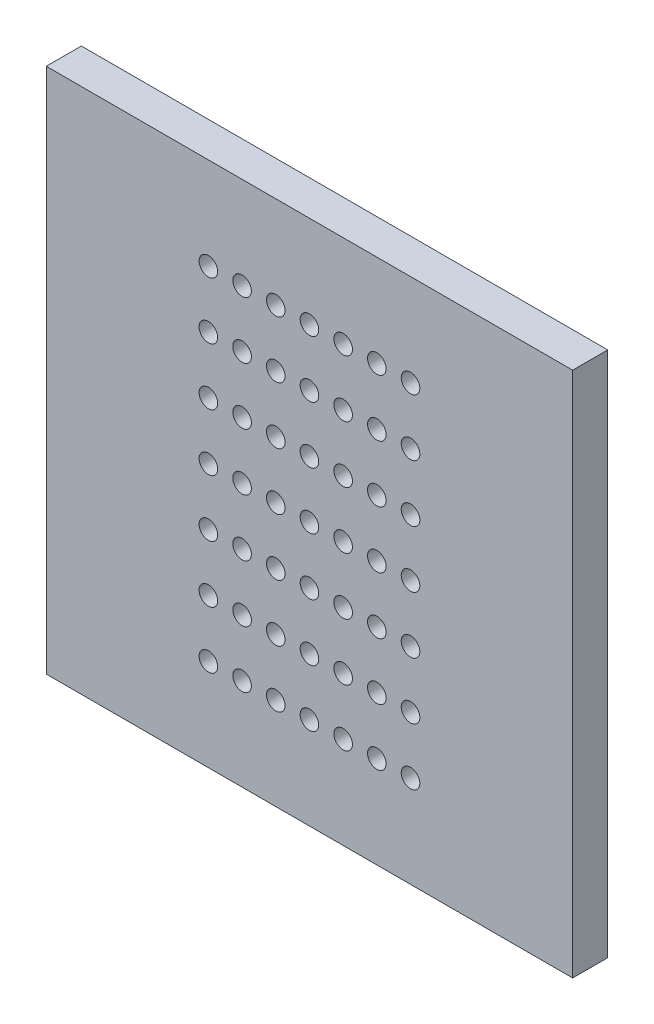
SolidWorks part; units mm, degrees
ref_plane "Plan de face" through (0, 0, 0) normal (0, 0, 1) x (1, 0, 0)
ref_plane "Plan de dessus" through (0, 0, 0) normal (0, 1, 0) x (1, 0, 0)
ref_plane "Plan de droite" through (0, 0, 0) normal (1, 0, 0) x (0, 0, -1)
sketch "Esquisse1" plane through (0, 0, 0) normal (0, 0, 1) x (1, 0, 0)
  line L1 (-15, -15) -> (15, -15)
  line L2 (-15, -15) -> (-15, 15)
  line L3 (-15, 15) -> (15, 15)
  line L4 (15, -15) -> (15, 15)
  line L5 (-15, -15) -> (15, 15) construction
  line L6 (-15, 15) -> (15, -15) construction
  point P0 (0, 0)
extrude "Base_Plate" add sketch "Esquisse1" along normal blind 2
sketch "Sketch_Perforations" plane through (0, 0, 2) normal (0, 0, 1) x (1, 0, 0)
  circle A0 centre (-5.76, -9.75) radius 0.53
  circle A1 centre (-5.76, -6.5) radius 0.53
  circle A2 centre (-5.76, -3.25) radius 0.53
  circle A3 centre (-5.76, 0) radius 0.53
  circle A4 centre (-5.76, 3.25) radius 0.53
  circle A5 centre (-5.76, 6.5) radius 0.53
  circle A6 centre (-5.76, 9.75) radius 0.53
  circle A7 centre (-3.84, -9.75) radius 0.53
  circle A8 centre (-3.84, -6.5) radius 0.53
  circle A9 centre (-3.84, -3.25) radius 0.53
  circle A10 centre (-3.84, 0) radius 0.53
  circle A11 centre (-3.84, 3.25) radius 0.53
  circle A12 centre (-3.84, 6.5) radius 0.53
  circle A13 centre (-3.84, 9.75) radius 0.53
  circle A14 centre (-1.92, -9.75) radius 0.53
  circle A15 centre (-1.92, -6.5) radius 0.53
  circle A16 centre (-1.92, -3.25) radius 0.53
  circle A17 centre (-1.92, 0) radius 0.53
  circle A18 centre (-1.92, 3.25) radius 0.53
  circle A19 centre (-1.92, 6.5) radius 0.53
  circle A20 centre (-1.92, 9.75) radius 0.53
  circle A21 centre (0, -9.75) radius 0.53
  circle A22 centre (0, -6.5) radius 0.53
  circle A23 centre (0, -3.25) radius 0.53
  circle A24 centre (0, 0) radius 0.53
  circle A25 centre (0, 3.25) radius 0.53
  circle A26 centre (0, 6.5) radius 0.53
  circle A27 centre (0, 9.75) radius 0.53
  circle A28 centre (1.92, -9.75) radius 0.53
  circle A29 centre (1.92, -6.5) radius 0.53
  circle A30 centre (1.92, -3.25) radius 0.53
  circle A31 centre (1.92, 0) radius 0.53
  circle A32 centre (1.92, 3.25) radius 0.53
  circle A33 centre (1.92, 6.5) radius 0.53
  circle A34 centre (1.92, 9.75) radius 0.53
  circle A35 centre (3.84, -9.75) radius 0.53
  circle A36 centre (3.84, -6.5) radius 0.53
  circle A37 centre (3.84, -3.25) radius 0.53
  circle A38 centre (3.84, 0) radius 0.53
  circle A39 centre (3.84, 3.25) radius 0.53
  circle A40 centre (3.84, 6.5) radius 0.53
  circle A41 centre (3.84, 9.75) radius 0.53
  circle A42 centre (5.76, -9.75) radius 0.53
  circle A43 centre (5.76, -6.5) radius 0.53
  circle A44 centre (5.76, -3.25) radius 0.53
  circle A45 centre (5.76, 0) radius 0.53
  circle A46 centre (5.76, 3.25) radius 0.53
  circle A47 centre (5.76, 6.5) radius 0.53
  circle A48 centre (5.76, 9.75) radius 0.53
extrude "Cut_Perforations" cut sketch "Sketch_Perforations" against normal blind 10
